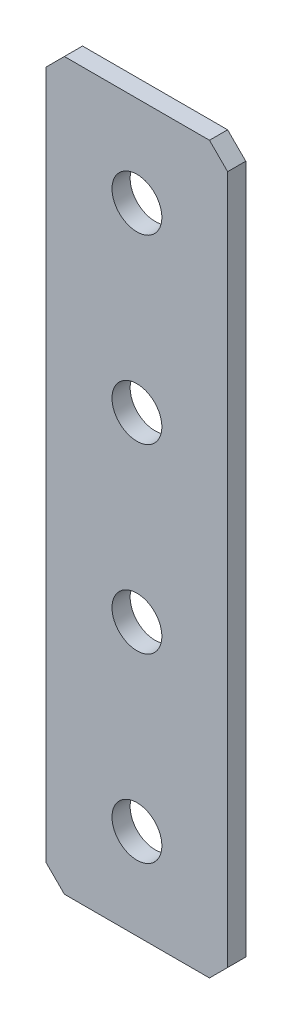
SolidWorks part; units mm, degrees
material "Простая углеродистая сталь"
ref_plane "Спереди(Плоскость XY)" through (0, 0, 0) normal (0, 0, 1) x (1, 0, 0)
ref_plane "Сверху(Плоскость XZ)" through (0, 0, 0) normal (0, 1, 0) x (1, 0, 0)
ref_plane "Справа(Плоскость ZY)" through (0, 0, 0) normal (1, 0, 0) x (0, 0, -1)
sketch "Эскиз1" plane through (0, 0, 0) normal (0, 0, 1) x (1, 0, 0)
  line L1 (-10, -40) -> (10, -40)
  line L2 (-10, -40) -> (-10, 40)
  line L3 (-10, 40) -> (10, 40)
  line L4 (10, -40) -> (10, 40)
  line L5 (-10, -40) -> (10, 40) construction
  line L6 (-10, 40) -> (10, -40) construction
  point P0 (0, 0)
  dimension "D1" = 20
  dimension "D2" = 80
extrude "Бобышка-Вытянуть1" add sketch "Эскиз1" along normal blind 2
chamfer "Фаска1" distance 2 angle 45 4 edges at (-10, -40, 1) (10, -40, 1) (-10, 40, 1) (10, 40, 1)
hole_wizard "Отверстие с зазором M51" positions "Эскиз2" profile "Эскиз3" hole size "M5" standard "DIN" end condition through all
sketch "Эскиз2" plane through (0, 0, 2) normal (0, 0, 1) x (1, 0, 0)
  line L12 (0, 40) -> (0, -40) construction
  line L13 (8, 40) -> (-8, 40) construction
  line L14 (-8, -40) -> (8, -40) construction
  point P204 (0, 30)
  point P206 (0, 10)
  point P208 (0, -10)
  point P210 (0, -30)
  dimension "D1" = 20
  dimension "D2" = 20
  dimension "D3" = 20
  dimension "D4" = 10
sketch "Эскиз3" plane through (0, -30, 2) normal (1, 0, 0) x (0, -1, 0)
  line L0 (0, 0) -> (0, 2)
  line L1 (0, 2) -> (2.75, 2)
  line L2 (2.75, 2) -> (2.75, 0)
  line L5 (2.75, 0) -> (0, 0)
  line L11 (0, -6.35) -> (0, 107.95) construction
  dimension "Диаметр сквозного отверстия" = 5.5
  dimension "Глубина сквозного отверстия" = 2
